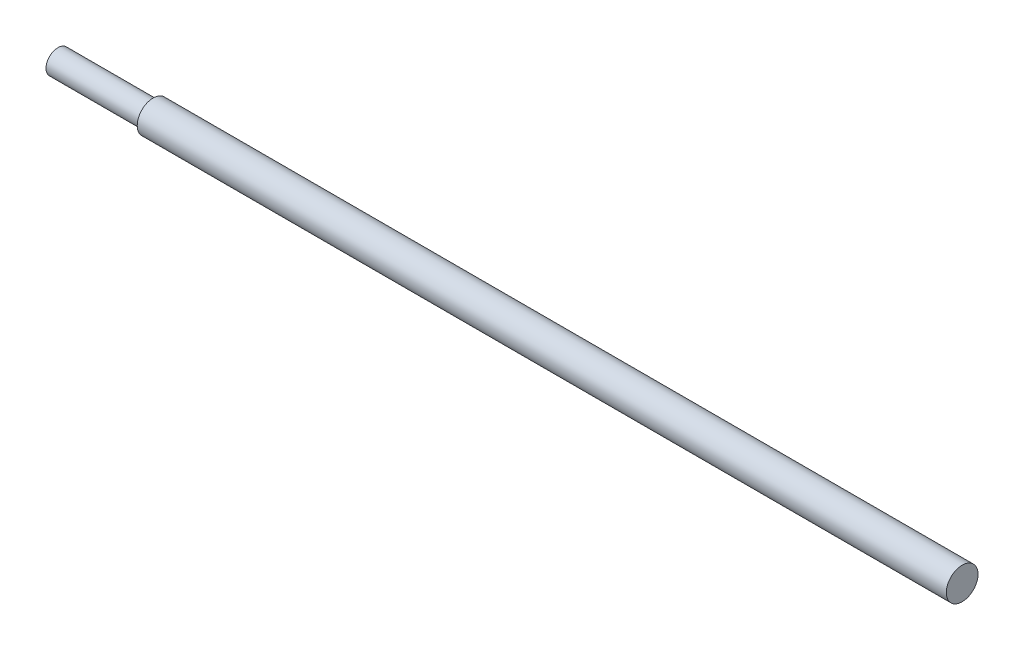
SolidWorks part; units mm, degrees
material "Plain Carbon Steel"
ref_plane "Front Plane" through (0, 0, 0) normal (0, 0, 1) x (1, 0, 0)
ref_plane "Top Plane" through (0, 0, 0) normal (0, 1, 0) x (1, 0, 0)
ref_plane "Right Plane" through (0, 0, 0) normal (1, 0, 0) x (0, 0, -1)
sketch "Sketch2" plane through (0, 0, 0) normal (0, 1, 0) x (1, 0, 0)
  line L0 (-723.9, 0) -> (723.9, 0)
  line L1 (-723.9, 0) -> (-723.9, 9.525)
  line L2 (-723.9, 9.525) -> (-647.7, 9.525)
  line L3 (-647.7, 9.525) -> (-647.7, 12.7)
  line L4 (-647.7, 12.7) -> (647.7, 12.7)
  line L5 (0, 12.7) -> (0, 0) construction
  line L6 (647.7, 9.525) -> (647.7, 12.7)
  line L7 (723.9, 9.525) -> (647.7, 9.525)
  line L8 (723.9, 0) -> (723.9, 9.525)
  line L9 (202.4736, 12.7) -> (202.4736, 0)
  point P4 (0, 0)
  dimension "D1" = 1447.8
  dimension "D2" = 9.525
  dimension "D3" = 12.7
  dimension "D4" = 76.2
revolve "Revolve1" add sketch "Sketch2" angle 360 about L0
sketch "Sketch3" plane through (0, 0, 0) normal (0, 1, 0) x (1, 0, 0)
  line L5 (-723.9, 0) -> (-411.48, 0) construction
  line L6 (-723.9, 9.525) -> (-723.9, -9.525) construction
  line L7 (-411.48, 0) -> (-411.48, 11.1125) construction
  line L8 (0, 12.7) -> (-647.7, 12.7) construction
  line L9 (-424.18, 9.525) -> (-398.78, 9.525)
  line L10 (-424.18, 9.525) -> (-424.18, 12.7)
  line L11 (-424.18, 12.7) -> (-398.78, 12.7)
  line L12 (-398.78, 9.525) -> (-398.78, 12.7)
  line L13 (-424.18, 9.525) -> (-398.78, 12.7) construction
  line L14 (-424.18, 12.7) -> (-398.78, 9.525) construction
  dimension "D1" = 312.42
  dimension "D2" = 25.4
  dimension "D3" = 3.175
extrude "Cut-Extrude1" cut sketch "Sketch3" against normal through all both and the other way through all
